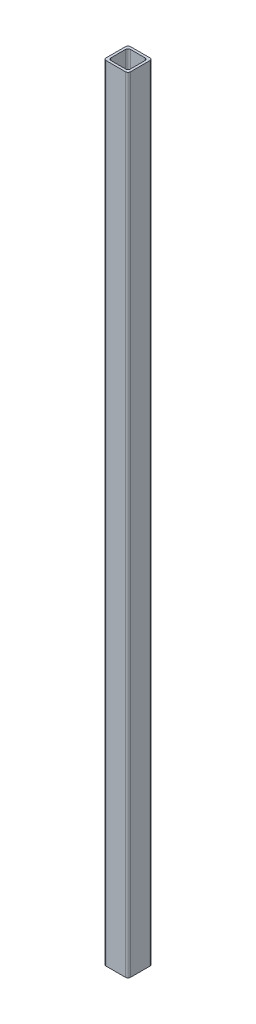
SolidWorks part; units mm, degrees
ref_plane "Front Plane" through (0, 0, 0) normal (0, 0, 1) x (1, 0, 0)
ref_plane "Top Plane" through (0, 0, 0) normal (0, 1, 0) x (1, 0, 0)
ref_plane "Right Plane" through (0, 0, 0) normal (1, 0, 0) x (0, 0, -1)
sketch "Sketch1" plane through (0, 0, 0) normal (0, 1, 0) x (1, 0, 0)
  line L1 (-8.5625, 4.2188) -> (1.4375, 4.2188)
  line L2 (-8.5625, 4.2188) -> (-8.5625, -5.7812)
  line L3 (-8.5625, -5.7812) -> (1.4375, -5.7812)
  line L4 (1.4375, 4.2188) -> (1.4375, -5.7812)
  dimension "D1" = 10
  dimension "D2" = 10
extrude "Boss-Extrude1" add sketch "Sketch1" along normal blind 310 contours L2 L1 L4 L3
sketch "Sketch2" plane through (0, 0, 0) normal (0, -1, 0) x (-1, 0, 0)
  line L0 (8.5625, -5.7812) -> (-1.4375, 4.2188)
  line L2 (7.5625, -4.7812) -> (-0.4375, -4.7812)
  line L3 (7.5625, -4.7812) -> (7.5625, 3.2188)
  line L4 (7.5625, 3.2188) -> (-0.4375, 3.2188)
  line L5 (-0.4375, -4.7812) -> (-0.4375, 3.2188)
  line L6 (7.5625, -4.7812) -> (-0.4375, 3.2188) construction
  line L7 (7.5625, 3.2188) -> (-0.4375, -4.7812) construction
  point P4 (3.5625, -0.7812)
  dimension "D1" = 8
extrude "Cut-Extrude1" cut sketch "Sketch2" against normal blind 310 contours L5 L2 L0 | L3 L4 L0
fillet "Fillet1" radius 1 4 edges at (-8.5625, 155, -4.2188) (0.4375, 155, -3.2188) (1.4375, 155, 5.7812) (-8.5625, 155, 5.7812)
fillet "Fillet2" radius 1 2 edges at (1.4375, 155, -4.2188) (-7.5625, 155, 4.7812)
fillet "Fillet3" radius 1 1 edges at (0.4375, 155, 4.7812)
fillet "Fillet4" radius 1 1 edges at (-7.5625, 155, -3.2188)
sketch "Sketch3" plane through (0, 310, 0) normal (0, 1, 0) x (1, 0, 0)
  line L0 (-7.5625, 4.2188) -> (0.4375, 4.2188)
  line L1 (1.4375, 3.2188) -> (1.4375, -4.7812)
  line L2 (0.4375, -5.7812) -> (-7.5625, -5.7812)
  line L3 (-8.5625, -4.7813) -> (-8.5625, 3.2187)
  arc A0 (1.4375, 3.2188) -> (0.4375, 4.2188) centre (0.4375, 3.2188) ccw construction
  arc A1 (-8.5625, -4.7812) -> (-7.5625, -5.7812) centre (-7.5625, -4.7812) ccw construction
  arc A2 (-8.5625, 3.2187) -> (-7.5625, 4.2188) centre (-7.5625, 3.2188) cw
  arc A3 (-7.5625, 2.2188) -> (-6.5625, 3.2188) centre (-6.5625, 2.2188) cw
  arc A4 (-0.5625, 3.2188) -> (0.4375, 2.2188) centre (-0.5625, 2.2188) cw
  arc A5 (0.4375, 4.2188) -> (1.4375, 3.2188) centre (0.4375, 3.2188) cw
  arc A6 (-0.5625, -4.7812) -> (0.4375, -3.7812) centre (-0.5625, -3.7812) ccw
  arc A7 (-0.5625, -4.7812) -> (0.4375, -3.7812) centre (-0.5625, -3.7812) ccw construction
  arc A8 (0.4375, -5.7812) -> (1.4375, -4.7812) centre (0.4375, -4.7812) ccw
  arc A9 (-7.5625, -5.7812) -> (-8.5625, -4.7813) centre (-7.5625, -4.7812) cw
  arc A10 (-7.5625, -3.7812) -> (-6.5625, -4.7812) centre (-6.5625, -3.7812) ccw
  line M1 (1.4375, -4.7812) -> (1.4375, 3.2188)
  arc M2 (1.4375, 3.2188) -> (0.4375, 4.2188) centre (0.4375, 3.2188) ccw
  line M3 (0.4375, 4.2188) -> (-7.5625, 4.2188)
  arc M4 (-7.5625, 4.2188) -> (-8.5625, 3.2188) centre (-7.5625, 3.2188) ccw
  line M5 (-8.5625, 3.2188) -> (-8.5625, -4.7812)
  arc M6 (-8.5625, -4.7812) -> (-7.5625, -5.7812) centre (-7.5625, -4.7812) ccw
  line M7 (-7.5625, -5.7812) -> (0.4375, -5.7812)
  arc M8 (0.4375, -5.7812) -> (1.4375, -4.7812) centre (0.4375, -4.7812) ccw
  line M9 (0.4375, 2.2188) -> (0.4375, -3.7812)
  arc M10 (0.4375, -3.7812) -> (-0.5625, -4.7812) centre (-0.5625, -3.7812) cw
  line M11 (-0.5625, -4.7812) -> (-6.5625, -4.7812)
  arc M12 (-6.5625, -4.7812) -> (-7.5625, -3.7812) centre (-6.5625, -3.7812) cw
  line M13 (-7.5625, -3.7812) -> (-7.5625, 2.2188)
  arc M14 (-7.5625, 2.2188) -> (-6.5625, 3.2188) centre (-6.5625, 2.2188) cw
  line M15 (-6.5625, 3.2188) -> (-0.5625, 3.2188)
  arc M16 (-0.5625, 3.2188) -> (0.4375, 2.2188) centre (-0.5625, 2.2188) cw
extrude "Boss-Extrude2" add sketch "Sketch3" along normal blind 42 contours M8 M1 M2 M3 M4 M5 M6 M7 M16 M9 M10 M11 M12 M13 M14 M15
sketch "Sketch4" plane through (0, 352, 0) normal (0, 1, 0) x (1, 0, 0)
  line L0 (-7.5625, 4.2188) -> (0.4375, 4.2188)
  line L1 (-0.5625, 3.2188) -> (-6.5625, 3.2188)
  line L2 (-7.5625, 2.2188) -> (-7.5625, -3.7812)
  line L3 (-6.5625, -4.7812) -> (-0.5625, -4.7812)
  line L4 (0.4375, -3.7812) -> (0.4375, 2.2188)
  line L5 (1.4375, 3.2188) -> (1.4375, -4.7812)
  line L6 (0.4375, -5.7812) -> (-7.5625, -5.7812)
  line L7 (-7.5625, -5.7812) -> (0.4375, -5.7812) construction
  line L8 (-8.5625, -4.7813) -> (-8.5625, 3.2187)
  arc A0 (0.4375, 2.2188) -> (-0.5625, 3.2188) centre (-0.5625, 2.2188) ccw construction
  arc A1 (-8.5625, -4.7812) -> (-7.5625, -5.7812) centre (-7.5625, -4.7812) ccw construction
  arc A2 (-8.5625, 3.2187) -> (-7.5625, 4.2188) centre (-7.5625, 3.2188) cw
  arc A3 (-7.5625, 2.2188) -> (-6.5625, 3.2188) centre (-6.5625, 2.2188) cw
  arc A4 (-0.5625, 3.2188) -> (0.4375, 2.2188) centre (-0.5625, 2.2188) cw
  arc A5 (0.4375, 4.2188) -> (1.4375, 3.2188) centre (0.4375, 3.2188) cw
  arc A6 (1.4375, -4.7812) -> (0.4375, -5.7812) centre (0.4375, -4.7812) cw
  arc A7 (-7.5625, -5.7812) -> (-8.5625, -4.7813) centre (-7.5625, -4.7812) cw
  arc A8 (-7.5625, -3.7812) -> (-6.5625, -4.7812) centre (-6.5625, -3.7812) ccw
  arc A9 (-0.5625, -4.7812) -> (0.4375, -3.7812) centre (-0.5625, -3.7812) ccw
  arc A10 (-0.5625, 3.2188) -> (0.4375, 2.2188) centre (-0.5625, 2.2188) cw
  arc A11 (-6.5625, 3.2188) -> (-7.5625, 2.2188) centre (-6.5625, 2.2188) ccw
  arc M9 (-0.5625, 3.2188) -> (0.4375, 2.2188) centre (-0.5625, 2.2188) cw
  line M10 (0.4375, 2.2188) -> (0.4375, -3.7812)
  arc M11 (0.4375, -3.7812) -> (-0.5625, -4.7812) centre (-0.5625, -3.7812) cw
  line M12 (-0.5625, -4.7812) -> (-6.5625, -4.7812)
  arc M13 (-6.5625, -4.7812) -> (-7.5625, -3.7812) centre (-6.5625, -3.7812) cw
  line M14 (-7.5625, -3.7812) -> (-7.5625, 2.2188)
  arc M15 (-7.5625, 2.2188) -> (-6.5625, 3.2188) centre (-6.5625, 2.2188) cw
  line M16 (-6.5625, 3.2188) -> (-0.5625, 3.2188)
  arc M17 (0.4375, -5.7812) -> (1.4375, -4.7812) centre (0.4375, -4.7812) ccw
  line M18 (1.4375, -4.7812) -> (1.4375, 3.2188)
  arc M19 (1.4375, 3.2188) -> (0.4375, 4.2188) centre (0.4375, 3.2188) ccw
  line M20 (0.4375, 4.2188) -> (-7.5625, 4.2188)
  arc M21 (-7.5625, 4.2188) -> (-8.5625, 3.2188) centre (-7.5625, 3.2188) ccw
  line M22 (-8.5625, 3.2188) -> (-8.5625, -4.7812)
  arc M23 (-8.5625, -4.7812) -> (-7.5625, -5.7812) centre (-7.5625, -4.7812) ccw
  line M24 (-7.5625, -5.7812) -> (0.4375, -5.7812)
extrude "Cut-Extrude2" cut sketch "Sketch4" against normal blind 35.07 contours M24 M17 M18 M19 M20 M21 M22 M23 M16 M9 M10 M11 M12 M13 M14 M15
sketch "Sketch6" plane through (0, 316.93, 0) normal (0, 1, 0) x (1, 0, 0)
  line L0 (0.4375, 3.2188) -> (-7.5625, 3.2188)
  line L1 (-7.5625, 3.2188) -> (-7.5625, -4.7812)
  line L2 (-7.5625, -4.7812) -> (0.4375, -4.7812)
  line L3 (0.4375, -4.7812) -> (0.4375, 3.2188)
  line L4 (-7.5625, -5.7812) -> (0.4375, -5.7812)
  line L5 (1.4375, -4.7812) -> (1.4375, 3.2188)
  line L6 (0.4375, 4.2188) -> (-7.5625, 4.2188)
  line L7 (-8.5625, 3.2188) -> (-8.5625, -4.7812)
  line L8 (-7.5625, -5.7812) -> (0.4375, -5.7812)
  line L9 (1.4375, -4.7812) -> (1.4375, 3.2188)
  line L10 (0.4375, 4.2188) -> (-7.5625, 4.2188)
  line L11 (-8.5625, 3.2188) -> (-8.5625, -4.7812)
  arc A0 (-7.5625, 3.2188) -> (-7.5625, 3.2188) centre (-7.5625, 3.2188) ccw
  arc A1 (-7.5625, -4.7812) -> (-7.5625, -4.7812) centre (-7.5625, -4.7812) ccw
  arc A2 (0.4375, -4.7812) -> (0.4375, -4.7812) centre (0.4375, -4.7812) ccw
  arc A3 (0.4375, 3.2188) -> (0.4375, 3.2188) centre (0.4375, 3.2188) ccw
  arc A4 (0.4375, -5.7812) -> (1.4375, -4.7812) centre (0.4375, -4.7812) ccw
  arc A5 (1.4375, 3.2188) -> (0.4375, 4.2188) centre (0.4375, 3.2188) ccw
  arc A6 (-7.5625, 4.2188) -> (-8.5625, 3.2188) centre (-7.5625, 3.2188) ccw
  arc A7 (-8.5625, -4.7812) -> (-7.5625, -5.7812) centre (-7.5625, -4.7812) ccw
  arc A8 (0.4375, -5.7812) -> (1.4375, -4.7812) centre (0.4375, -4.7812) ccw
  arc A9 (1.4375, 3.2188) -> (0.4375, 4.2188) centre (0.4375, 3.2188) ccw
  arc A10 (-7.5625, 4.2188) -> (-8.5625, 3.2188) centre (-7.5625, 3.2188) ccw
  arc A11 (-8.5625, -4.7812) -> (-7.5625, -5.7812) centre (-7.5625, -4.7812) ccw
  dimension "D1" = 0
  dimension "D2" = 1
extrude "Cut-Extrude3" cut sketch "Sketch6" against normal blind 2 contours L8 A8 L9 A9 L10 A10 L11 A11
sketch "Sketch7" plane through (0, 314.93, 0) normal (0, 1, 0) x (1, 0, 0)
  line L0 (-6.5625, 3.2188) -> (-0.5625, 3.2188)
  line L1 (0.4375, 2.2188) -> (0.4375, -3.7812)
  line L2 (-0.5625, -4.7812) -> (-6.5625, -4.7812)
  line L3 (-7.5625, -3.7812) -> (-7.5625, 2.2187)
  line L4 (-8.5625, 3.2187) -> (-8.5625, -4.7813)
  line L5 (-7.5625, -5.7812) -> (0.4375, -5.7812)
  line L6 (1.4375, -4.7812) -> (1.4375, 3.2188)
  line L7 (0.4375, 4.2188) -> (-7.5625, 4.2188)
  arc A0 (-8.5625, 3.2187) -> (-7.5625, 4.2188) centre (-7.5625, 3.2188) cw
  arc A1 (-7.5625, 2.2187) -> (-6.5625, 3.2188) centre (-6.5625, 2.2188) cw
  arc A2 (-0.5625, 3.2188) -> (0.4375, 2.2188) centre (-0.5625, 2.2188) cw
  arc A3 (0.4375, 4.2188) -> (1.4375, 3.2188) centre (0.4375, 3.2188) cw
  arc A4 (-0.5625, -4.7812) -> (0.4375, -3.7812) centre (-0.5625, -3.7812) ccw
  arc A5 (0.4375, -5.7812) -> (1.4375, -4.7812) centre (0.4375, -4.7812) ccw
  arc A6 (-7.5625, -5.7812) -> (-8.5625, -4.7813) centre (-7.5625, -4.7812) cw
  arc A7 (-7.5625, -3.7812) -> (-6.5625, -4.7812) centre (-6.5625, -3.7812) ccw
extrude "Boss-Extrude4" add sketch "Sketch7" against normal blind 370 contours A6 L4 A0 L7 A3 L6 A5 L5 | A7 L2 A4 L1 A2 L0 A1 L3
sketch "Sketch13" plane through (0, -55.07, 0) normal (0, -1, 0) x (-1, 0, 0)
  line L0 (7.5625, -5.7812) -> (-0.4375, 4.2188)
  line L1 (-0.4375, 4.2188) -> (7.5625, 4.2188) construction
  line L2 (3.5625, 4.2188) -> (3.5625, -0.7812)
  line L4 (7.5625, 3.2188) -> (-0.4375, 3.2188)
  line L5 (7.5625, 3.2188) -> (7.5625, -4.7812)
  line L6 (7.5625, -4.7812) -> (-0.4375, -4.7812)
  line L7 (-0.4375, 3.2188) -> (-0.4375, -4.7812)
  line L8 (7.5625, 3.2188) -> (-0.4375, -4.7812) construction
  line L9 (7.5625, -4.7812) -> (-0.4375, 3.2188) construction
  line L10 (8.5625, -5.7812) -> (-1.4375, -5.7812)
  line L11 (8.5625, -5.7812) -> (8.5625, 4.2188)
  line L12 (8.5625, 4.2188) -> (-1.4375, 4.2188)
  line L13 (-1.4375, -5.7812) -> (-1.4375, 4.2188)
  line L14 (8.5625, -5.7812) -> (-1.4375, 4.2188) construction
  line L15 (8.5625, 4.2188) -> (-1.4375, -5.7812) construction
  arc A0 (-0.4375, 4.2188) -> (-1.4375, 3.2188) centre (-0.4375, 3.2188) ccw construction
  line M7 (-0.4375, -5.7812) -> (7.5625, -5.7812)
  arc M8 (7.5625, -5.7812) -> (8.5625, -4.7813) centre (7.5625, -4.7812) ccw
  line M9 (8.5625, -4.7813) -> (8.5625, 3.2187)
  arc M10 (8.5625, 3.2187) -> (7.5625, 4.2188) centre (7.5625, 3.2188) ccw
  line M11 (7.5625, 4.2188) -> (-0.4375, 4.2188)
  arc M12 (-0.4375, 4.2188) -> (-1.4375, 3.2188) centre (-0.4375, 3.2188) ccw
  line M13 (-1.4375, 3.2188) -> (-1.4375, -4.7812)
  arc M14 (-1.4375, -4.7812) -> (-0.4375, -5.7812) centre (-0.4375, -4.7812) ccw
  line M15 (7.5625, 2.2187) -> (7.5625, -3.7812)
  line M17 (6.5625, -4.7812) -> (0.5625, -4.7812)
  line M19 (-0.4375, -3.7812) -> (-0.4375, 2.2188)
  line M21 (0.5625, 3.2188) -> (6.5625, 3.2188)
  dimension "D1" = 8
  dimension "D2" = 8
  dimension "D3" = 10
  dimension "D4" = 10
extrude "Cut-Extrude4" cut sketch "Sketch13" against normal blind 46.92 contours L5 L6 L0 L2 L4 M8 M9 M10 M11 M21 M15 | L7 L4 L0 L6 M12 M13 M14 M7 M17 M19 | L4 L2 L0 M21 M11
sketch "Sketch14" plane through (0.4375, 0, 0) normal (1, 0, 0) x (0, 0, -1)
  line L1 (-4.7812, -55.07) -> (-3.7812, -55.07)
  line L2 (-4.7812, -55.07) -> (-4.7812, -8.15)
  line L3 (-4.7812, -8.15) -> (-3.7812, -8.15)
  line L4 (-3.7812, -55.07) -> (-3.7812, -8.15)
  line L5 (3.2188, -8.15) -> (2.2188, -8.15)
  line L6 (3.2188, -8.15) -> (3.2188, -55.07)
  line L7 (3.2188, -55.07) -> (2.2188, -55.07)
  line L8 (2.2188, -8.15) -> (2.2188, -55.07)
extrude "Cut-Extrude5" cut sketch "Sketch14" against normal blind 46.92 contours L2 L1 L4 L3 | L6 L5 L8 L7
